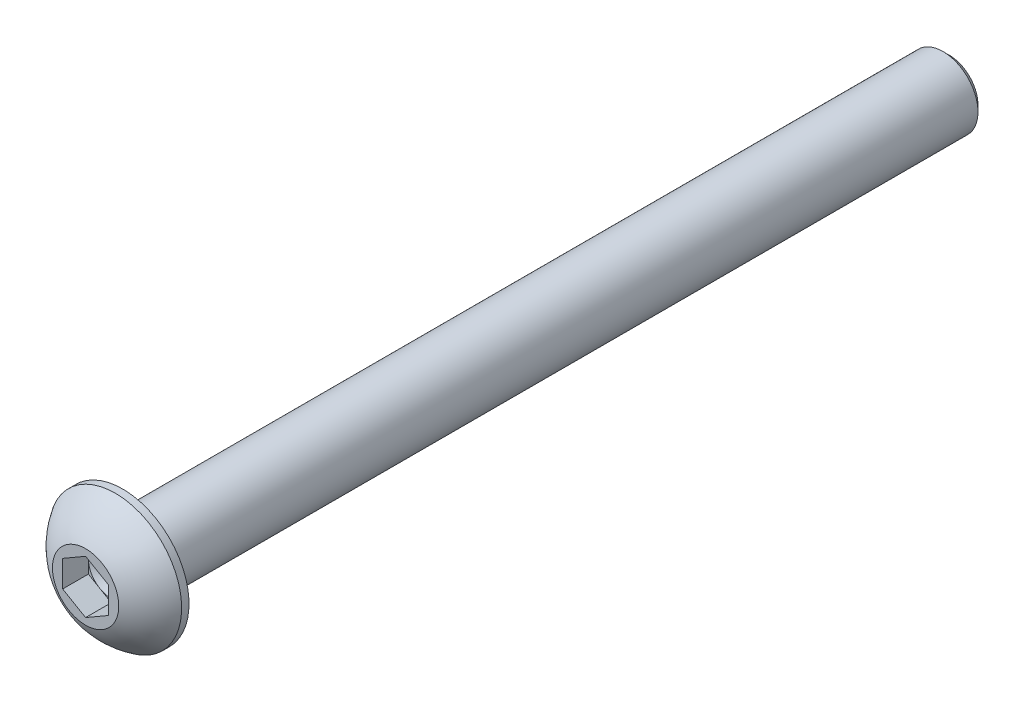
SolidWorks part; units mm, degrees
material "6061 Alloy"
ref_plane "Front Plane" through (0, 0, 0) normal (0, 0, 1) x (1, 0, 0)
ref_plane "Top Plane" through (0, 0, 0) normal (0, 1, 0) x (1, 0, 0)
ref_plane "Right Plane" through (0, 0, 0) normal (1, 0, 0) x (0, 0, -1)
ref_plane "Plane1" through (0, 0, 0) normal (0, -1, 0) x (1, 0, 0)
sketch "Sketch1" plane through (0, 0, 0) normal (0, -1, 0) x (1, 0, 0)
  line L0 (2.2923, 0) -> (0, 0)
  line L1 (0, 0) -> (0, -2.5654)
  line L2 (0, -2.5654) -> (4.5847, -2.5654)
  line L3 (4.5847, -2.5654) -> (4.5847, -2.0574)
  line L4 (0, 0) -> (0, -2.5654) construction
  arc A0 (4.5847, -2.0574) -> (2.2923, 0) centre (0, -4.8599) ccw
  dimension "D1" = 5.3734
  dimension "D2" = 2.2923
  dimension "D3" = 4.5847
  dimension "D4" = 2.5654
revolve "Revolve1" add sketch "Sketch1" angle 360 about L4
sketch "Sketch2" plane through (0, 0, -2.5654) normal (0, 0, -1) x (-1, 0, 0)
  circle A0 centre (0, 0) radius 2.413
  dimension "D1" = 4.826
extrude "Boss-Extrude1" add sketch "Sketch2" along normal blind 57.15
sketch "Sketch3" plane through (0, 0, 0) normal (0, 0, 1) x (1, 0, 0)
  line L0 (1.5875, -0.9165) -> (1.5875, 0.9165)
  line L1 (1.5875, 0.9165) -> (0, 1.8331)
  line L2 (0, 1.8331) -> (-1.5875, 0.9165)
  line L3 (-1.5875, 0.9165) -> (-1.5875, -0.9165)
  line L4 (-1.5875, -0.9165) -> (0, -1.8331)
  line L5 (0, -1.8331) -> (1.5875, -0.9165)
  circle A0 centre (0, 0) radius 2.2923 construction
  dimension "D1" = 1.5875
  dimension "D2" = 1.5875
  dimension "D3" = 0.9165
  dimension "D4" = 1.8331
  dimension "D5" = 0.9165
  dimension "D6" = 1.8331
extrude "Cut-Extrude1" cut sketch "Sketch3" against normal blind 1.778
sketch "Sketch4" plane through (0, 0, 0) normal (0, -1, 0) x (1, 0, 0)
  line L0 (1.5875, -1.778) -> (0, -1.778)
  line L1 (0, -1.778) -> (0, -2.6945)
  line L2 (0, -2.6945) -> (1.5875, -1.778)
  line L3 (0, -1.778) -> (0, -2.6945) construction
  dimension "D1" = 1.5875
  dimension "D2" = 0.9165
revolve "Cut-Revolve1" cut sketch "Sketch4" angle 360 about L3
chamfer "Chamfer1" distance 0.4289 angle 45 1 edges at (-2.413, 0, -59.7154)
fillet "Fillet1" radius 0.381 1 edges at (-2.413, 0, -2.5654)
